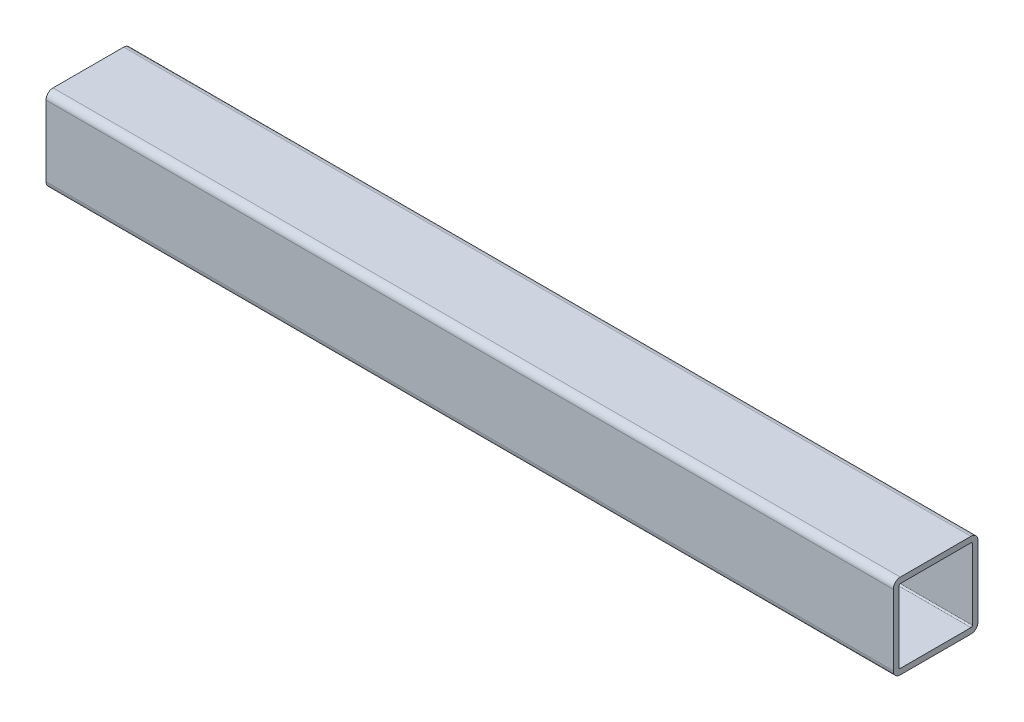
SolidWorks part; units mm, degrees
ref_plane "Front Plane" through (0, 0, 0) normal (0, 0, 1) x (1, 0, 0)
ref_plane "Top Plane" through (0, 0, 0) normal (0, 1, 0) x (1, 0, 0)
ref_plane "Right Plane" through (0, 0, 0) normal (1, 0, 0) x (0, 0, -1)
sketch "Sketch1" plane through (0, 0, 0) normal (1, 0, 0) x (0, 0, -1)
  line L1 (-15.875, 19.05) -> (15.875, 19.05)
  line L2 (-19.05, 15.875) -> (-19.05, -15.875)
  line L3 (-15.875, -19.05) -> (15.875, -19.05)
  line L4 (19.05, 15.875) -> (19.05, -15.875)
  line L5 (-19.05, 19.05) -> (19.05, -19.05) construction
  line L6 (-19.05, -19.05) -> (19.05, 19.05) construction
  arc A0 (-19.05, -15.875) -> (-15.875, -19.05) centre (-15.875, -15.875) ccw
  arc A1 (15.875, -19.05) -> (19.05, -15.875) centre (15.875, -15.875) ccw
  arc A2 (19.05, 15.875) -> (15.875, 19.05) centre (15.875, 15.875) ccw
  arc A3 (-15.875, 19.05) -> (-19.05, 15.875) centre (-15.875, 15.875) ccw
  point P0 (0, 0)
  dimension "D3" = 3.175
  dimension "D1" = 38.1
  dimension "D2" = 38.1
extrude "Extrude-Thin1" add sketch "Sketch1" along normal mid plane 381 thin
sketch "Sketch7" plane through (190.5, 0, 0) normal (1, 0, 0) x (0, 0, -1)
  line L0 (16.51, 0) -> (-16.51, 0) construction
  line L1 (16.51, -15.875) -> (16.51, 15.875) construction
  line L2 (-16.51, 15.875) -> (-16.51, -15.875) construction
  line L3 (0, 16.51) -> (0, -16.51) construction
  line L4 (15.875, 16.51) -> (-15.875, 16.51) construction
  line L5 (-15.875, -16.51) -> (15.875, -16.51) construction
sketch "Sketch9" plane through (-190.5, 0, 0) normal (-1, 0, 0) x (0, 0, 1)
  line L0 (0, 16.51) -> (0, -16.51) construction
  line L1 (-15.875, 16.51) -> (15.875, 16.51) construction
  line L2 (15.875, -16.51) -> (-15.875, -16.51) construction
  line L3 (16.51, 0) -> (-16.51, 0) construction
  line L4 (16.51, 15.875) -> (16.51, -15.875) construction
  line L5 (-16.51, -15.875) -> (-16.51, 15.875) construction
